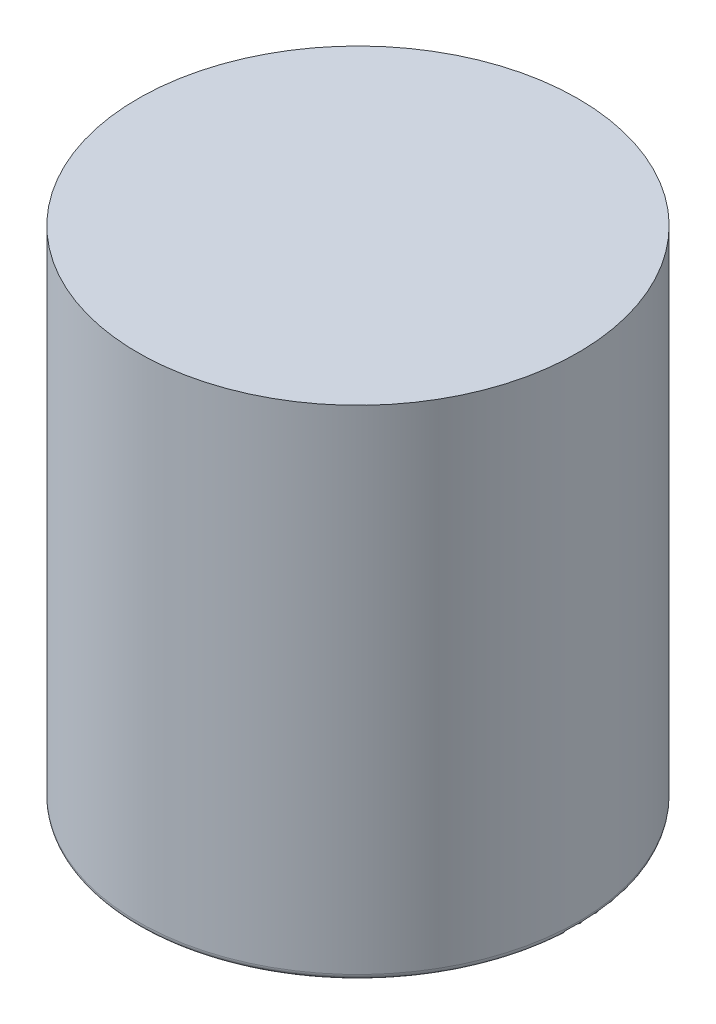
SolidWorks part; units mm, degrees
ref_plane "前视基准面" through (0, 0, 0) normal (0, 0, 1) x (1, 0, 0)
ref_plane "上视基准面" through (0, 0, 0) normal (0, 1, 0) x (1, 0, 0)
ref_plane "右视基准面" through (0, 0, 0) normal (1, 0, 0) x (0, 0, -1)
sketch "草图1" plane through (0, 0, 0) normal (0, 0, 1) x (1, 0, 0)
  line L0 (0, -19.8404) -> (0, 10.1145) construction
  line L1 (3.5, -11.0995) -> (7.5, -11.0995)
  line L2 (7.5, -11.0995) -> (7.5, 5.9005)
  line L3 (7.5, 5.9005) -> (0, 5.9005)
  dimension "D1" = 7.5
  dimension "D2" = 3.5
  dimension "D3" = 17
revolve "旋转-薄壁1" add sketch "草图1" angle 360 about L0 wall 0.6
hole_wizard "M2 螺纹孔1" positions "草图2" profile "草图3" tap size "M2" standard "GB"
sketch "草图2" plane through (0, -11.0995, 0) normal (0, -1, 0) x (-1, 0, 0)
  line L0 (0, 8.25) -> (0, -8.25) construction
  point P0 (0, 5.4397)
sketch "草图3" plane through (0, -11.0995, -5.4397) normal (1, 0, 0) x (0, 0, -1)
  line L0 (0, 0) -> (0, 2.4807)
  line L1 (0, 2.4807) -> (0.8, 2)
  line L2 (0.8, 2) -> (0.8, 0)
  line L5 (0.8, 0) -> (0, 0)
  line L10 (0, 2.4807) -> (-0.8, 2) construction
  line L11 (0, -6.35) -> (0, 107.95) construction
  dimension "螺纹孔钻头直径" = 1.6
  dimension "螺纹孔钻头深度" = 2
  dimension "导头角度" = 118
cosmetic thread "孔螺蚊线1" parameters "D1"=0.6, "D2"=2
mirror "镜向1" about plane through (0, 0, 0) normal (0, 0, 1) of "M2 螺纹孔1"
fillet "圆角1" radius 0.2 1 edges at (0, -11.0995, -7.5)
